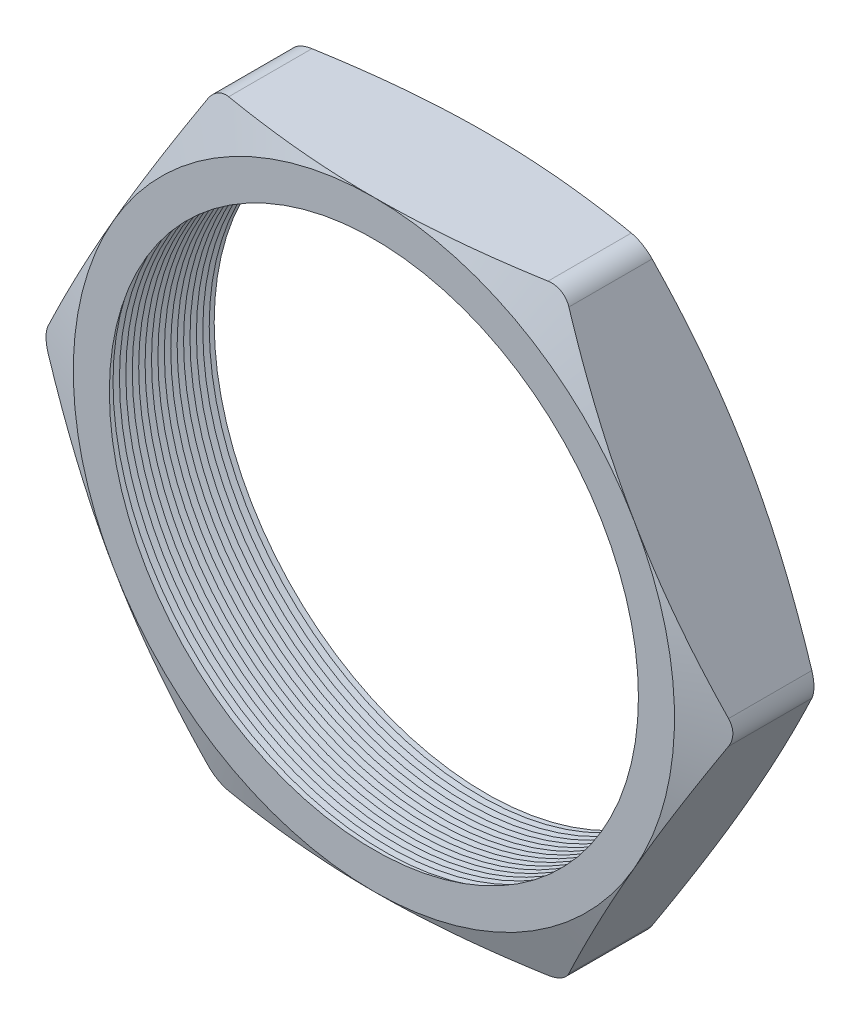
SolidWorks part; units mm, degrees
ref_plane "Front Plane" through (0, 0, 0) normal (0, 0, 1) x (1, 0, 0)
ref_plane "Top Plane" through (0, 0, 0) normal (0, 1, 0) x (1, 0, 0)
ref_plane "Right Plane" through (0, 0, 0) normal (1, 0, 0) x (0, 0, -1)
sketch "Sketch1" plane through (0, 0, 0) normal (0, 0, 1) x (1, 0, 0)
  line L1 (-10.9985, 0) -> (-5.4993, -9.525)
  line L2 (-5.4993, -9.525) -> (5.4993, -9.525)
  line L3 (5.4993, -9.525) -> (10.9985, 0)
  line L4 (10.9985, 0) -> (5.4993, 9.525)
  line L5 (5.4993, 9.525) -> (-5.4993, 9.525)
  line L6 (-5.4993, 9.525) -> (-10.9985, 0)
  circle A0 centre (0, 0) radius 9.525 construction
  circle A1 centre (0, 0) radius 8.382
  dimension "TS" = 16.764
  dimension "H" = 19.05
extrude "Extrude1" add sketch "Sketch1" along normal blind 3.556
fillet "Fillet1" radius 0.762 6 edges at (-5.4993, 9.525, 1.778) (-10.9985, 0, 1.778) (-5.4993, -9.525, 1.778) (5.4993, -9.525, 1.778) (10.9985, 0, 1.778) (5.4993, 9.525, 1.778)
sketch "Sketch2" plane through (0, 0, 3.556) normal (0, 0, 1) x (1, 0, 0)
  line L0 (5.0593, 9.525) -> (-5.0593, 9.525) construction
  circle A0 centre (0, 0) radius 9.525
extrude "Cut-Extrude1" cut sketch "Sketch2" against normal through all draft 70 flip side to cut
sketch "Sketch3" plane through (0, 0, 0) normal (0, 0, -1) x (-1, 0, 0)
  circle A0 centre (0, 0) radius 9.525
extrude "Cut-Extrude2" cut sketch "Sketch3" against normal through all draft 70 flip side to cut
sketch "Sketch4" plane through (0, 0, 0) normal (0, 1, 0) x (1, 0, 0)
  line L0 (-8.382, -3.556) -> (-8.382, -3.1161)
  line L2 (-8.382, -3.1161) -> (-8.763, -3.336)
  line L3 (-8.763, -3.336) -> (-8.382, -3.556)
  line L5 (-8.382, 0) -> (-8.382, -3.556) construction
  line L6 (-8.382, -3.556) -> (8.382, -3.556) construction
  dimension "D1" = 60
  dimension "D2" = 60
  dimension "D3" = 0.381
revolve "Cut-Revolve1" cut sketch "Sketch4" angle 360 about axis through (0, 0, 3.556) along (0, 0, -1)
pattern_linear "LPattern1" count 18 spacing 0.2032 along (0, 0, -1) of "Cut-Revolve1"
